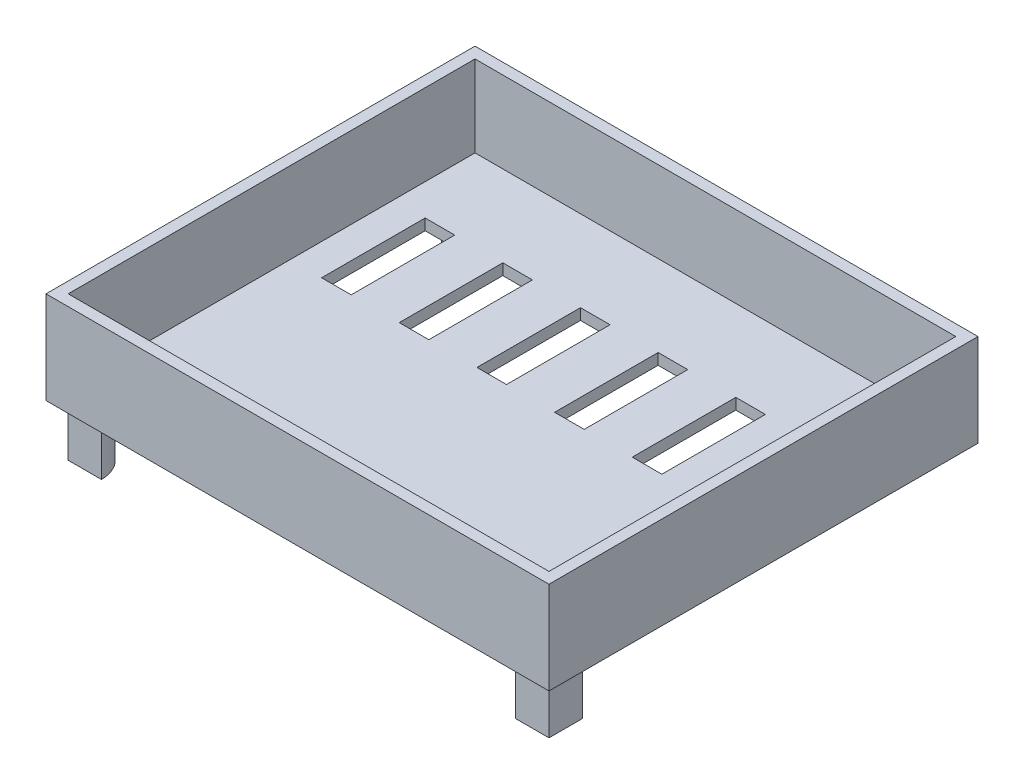
SolidWorks part; units mm, degrees
ref_plane "Front Plane" through (0, 0, 0) normal (0, 0, 1) x (1, 0, 0)
ref_plane "Top Plane" through (0, 0, 0) normal (0, 1, 0) x (1, 0, 0)
ref_plane "Right Plane" through (0, 0, 0) normal (1, 0, 0) x (0, 0, -1)
sketch "Sketch2" plane through (0, 0, 0) normal (0, 1, 0) x (1, 0, 0)
  line L1 (-58.7009, 58.1197) -> (77.2991, 58.1197)
  line L2 (-58.7009, 58.1197) -> (-58.7009, -77.8803)
  line L3 (-58.7009, -77.8803) -> (77.2991, -77.8803)
  line L4 (77.2991, 58.1197) -> (77.2991, -77.8803)
  dimension "D1" = 136
  dimension "D2" = 136
extrude "Boss-Extrude1" add sketch "Sketch2" along normal blind 25
sketch "Sketch3" plane through (0, 25, 0) normal (0, 1, 0) x (1, 0, 0)
  line L9 (-49.7009, -68.8803) -> (68.2991, -68.8803)
  line L10 (-49.7009, -68.8803) -> (-49.7009, 49.1197)
  line L11 (-49.7009, 49.1197) -> (68.2991, 49.1197)
  line L12 (68.2991, -68.8803) -> (68.2991, 49.1197)
extrude "Cut-Extrude1" cut sketch "Sketch3" against normal blind 22
sketch "Sketch4" plane through (0, 25, 0) normal (0, 1, 0) x (1, 0, 0)
  line L0 (77.2991, -77.8803) -> (47.2991, -77.8803)
  line L1 (-58.7009, -77.8803) -> (77.2991, -77.8803) construction
  line L2 (77.2991, -77.8803) -> (77.2991, -47.8803)
  line L3 (77.2991, -77.8803) -> (77.2991, 58.1197) construction
  line L4 (56.2991, -68.8803) -> (68.2991, -56.8803)
  line L5 (47.2991, -77.8803) -> (47.2991, -68.8803)
  line L6 (-49.7009, -68.8803) -> (68.2991, -68.8803) construction
  line L7 (47.2991, -68.8803) -> (56.2991, -68.8803)
  line L8 (77.2991, -47.8803) -> (68.2991, -47.8803)
  line L9 (68.2991, -68.8803) -> (68.2991, 49.1197) construction
  line L10 (68.2991, -47.8803) -> (68.2991, -56.8803)
extrude "Cut-Extrude3" cut sketch "Sketch4" against normal blind 22
sketch "Sketch5" plane through (0, 3, 0) normal (0, 1, 0) x (1, 0, 0)
  line L0 (68.2991, -47.8803) -> (47.2991, -68.8803)
  line L1 (47.2991, -68.8803) -> (47.2991, -77.8803)
  line L2 (47.2991, -77.8803) -> (77.2991, -77.8803)
  line L3 (77.2991, -77.8803) -> (77.2991, -47.8803)
  line L4 (77.2991, -47.8803) -> (68.2991, -47.8803)
extrude "Cut-Extrude4" cut sketch "Sketch5" against normal blind 22
sketch "Sketch7" plane through (58.0897, 0, 58.0897) normal (0.7071, 0, 0.7071) x (0.7071, 0, -0.7071)
  line L0 (-15.2602, 3) -> (14.4383, 3)
  line L1 (-15.2602, 3) -> (-15.2602, -27.0039)
  line L2 (14.4383, 3) -> (14.4383, -27.0039)
  line L3 (-15.2602, -27.0039) -> (14.4383, -27.0039)
extrude "Boss-Extrude2" add sketch "Sketch7" along normal blind 25
sketch "Sketch8" plane through (0, 3, 0) normal (0, 1, 0) x (1, 0, 0)
  line L0 (47.2991, -77.8803) -> (77.2991, -47.8803)
  line L1 (77.2991, -47.8803) -> (68.2991, -47.8803)
  line L2 (68.2991, -47.8803) -> (47.2991, -68.8803)
  line L3 (47.2991, -68.8803) -> (47.2991, -77.8803)
extrude "Boss-Extrude3" add sketch "Sketch8" against normal blind 3
sketch "Sketch9" plane through (0, 3, 0) normal (0, 1, 0) x (1, 0, 0)
  line L0 (47.2991, -77.8803) -> (38.2991, -68.8803)
  line L1 (-49.7009, -68.8803) -> (47.2991, -68.8803) construction
  line L2 (38.2991, -68.8803) -> (47.2991, -68.8803)
  line L3 (47.2991, -68.8803) -> (47.2991, -77.8803)
extrude "Cut-Extrude5" cut sketch "Sketch9" along normal blind 23
sketch "Sketch10" plane through (0, 25, 0) normal (0, 1, 0) x (1, 0, 0)
  line L0 (77.2991, -47.8803) -> (68.2991, -38.8803)
  line L1 (68.2991, -47.8803) -> (68.2991, 49.1197) construction
  line L2 (68.2991, -38.8803) -> (68.2991, -47.8803)
  line L3 (68.2991, -47.8803) -> (77.2991, -47.8803)
extrude "Cut-Extrude6" cut sketch "Sketch10" against normal blind 22
sketch "Sketch11" plane through (-10.7906, 0, 10.7906) normal (-0.7071, 0, 0.7071) x (0.7071, 0, 0.7071)
  line L0 (88.5153, 0) -> (107.1513, -18.636)
  line L1 (107.1513, 3) -> (107.1513, -27.0039) construction
  line L2 (107.1513, -18.636) -> (107.1513, -27.0039)
  line L3 (107.1513, -27.0039) -> (82.1513, -27.0039)
  line L4 (82.1513, -27.0039) -> (82.1513, 0)
  line L5 (82.1513, 0) -> (88.5153, 0)
  line L6 (88.5153, 3) -> (107.1513, -15.636)
  line L7 (107.1513, -15.636) -> (107.1513, 3)
  line L8 (107.1513, 3) -> (88.5153, 3)
extrude "Cut-Extrude7" cut sketch "Sketch11" against normal blind 32
sketch "Sketch16" plane through (-10.7906, 0, 10.7906) normal (-0.7071, 0, 0.7071) x (0.7071, 0, 0.7071)
  line L0 (88.5153, 0) -> (88.5153, 3)
  line L1 (88.5153, 3) -> (107.1513, -15.636)
  line L2 (107.1513, -15.636) -> (107.1513, -18.636)
  line L3 (107.1513, -18.636) -> (88.5153, 0)
extrude "Boss-Extrude6" add sketch "Sketch16" along normal blind 6.36
sketch "Sketch17" plane through (10.2094, 0, -10.2094) normal (0.7071, 0, -0.7071) x (-0.7071, 0, -0.7071)
  line L4 (-88.5153, 0) -> (-88.5153, 3)
  line L5 (-88.5153, 3) -> (-107.1513, -15.636)
  line L6 (-107.1513, -15.636) -> (-107.1513, -18.636)
  line L7 (-107.1513, -18.636) -> (-88.5153, 0)
  line L8 (-88.5153, 0) -> (-88.5153, 3)
  line L9 (-88.5153, 3) -> (-107.1513, -15.636)
  line L10 (-107.1513, -15.636) -> (-107.1513, -18.636)
  line L11 (-107.1513, -18.636) -> (-88.5153, 0)
  dimension "D1" = 0
extrude "Boss-Extrude7" add sketch "Sketch17" along normal blind 6.36
sketch "Sketch18" plane through (32.3555, 45.7576, 32.3555) normal (0.5, 0.7071, 0.5) x (0.866, -0.4082, -0.2887)
  line L0 (51.8932, -37.3644) -> (67.1094, -58.8834)
  line L1 (61.9165, -62.5554) -> (51.8932, -37.3644)
  line L3 (67.1094, -58.8834) -> (61.9165, -62.5554)
  line L4 (67.1094, -58.8834) -> (32.4749, -83.3737) construction
  line L5 (32.4749, -83.3737) -> (37.6678, -79.7018)
  line L6 (32.4749, -83.3737) -> (17.2586, -61.8547)
  line L7 (17.2586, -61.8547) -> (37.6678, -79.7018)
extrude "Cut-Extrude9" cut sketch "Sketch18" against normal blind 6.36
sketch "Sketch19" plane through (-15.2878, 0, 15.2878) normal (-0.7071, 0, 0.7071) x (0.7071, 0, 0.7071)
  line L3 (107.1513, -18.636) -> (107.1513, -15.636)
  line L4 (107.1513, -15.636) -> (105.6513, -17.136)
  line L5 (105.6513, -17.136) -> (107.1513, -18.636)
  line L6 (107.1513, -18.636) -> (107.1513, -15.636)
  line L7 (107.1513, -15.636) -> (105.6513, -17.136)
  line L8 (105.6513, -17.136) -> (107.1513, -18.636)
  dimension "D1" = 0
extrude "Cut-Extrude10" cut sketch "Sketch19" against normal blind 56.36
sketch "Sketch20" plane through (0, 0, 0) normal (0, -1, 0) x (1, 0, 0)
  line L0 (-58.7009, 77.8803) -> (47.2991, 77.8803)
  line L1 (47.2991, 77.8803) -> (77.2991, 47.8803)
  line L2 (77.2991, 47.8803) -> (77.2991, -58.1197)
  line L3 (77.2991, -58.1197) -> (-58.7009, -58.1197)
  line L4 (-58.7009, -58.1197) -> (-58.7009, 77.8803)
extrude "Boss-Extrude8" add sketch "Sketch20" against normal blind 3
sketch "Sketch22" plane through (0, 3, 0) normal (0, 1, 0) x (1, 0, 0)
  line L0 (64.9768, -86.558) -> (70.9062, -91.9285)
  line L1 (85.9768, -65.558) -> (91.9062, -70.9285)
  line L2 (70.9062, -91.9285) -> (91.9062, -70.9285)
  line L3 (64.9768, -86.558) -> (85.9768, -65.558)
extrude "Boss-Extrude9" add sketch "Sketch22" along normal blind 2 from offset 20 separate body offset against normal yes
sketch "Sketch23" plane through (75.7674, 0, 75.7674) normal (-0.7071, 0, -0.7071) x (-0.7071, 0, 0.7071)
  line L4 (-14.4383, -17) -> (15.2602, -17)
  line L5 (15.2602, -17) -> (15.2602, -15)
  line L6 (15.2602, -15) -> (-14.4383, -15)
  line L7 (-14.4383, -15) -> (-14.4383, -17)
  line L8 (-14.4383, -17) -> (15.2602, -17)
  line L9 (15.2602, -17) -> (15.2602, -15)
  line L10 (15.2602, -15) -> (-14.4383, -15)
  line L11 (-14.4383, -15) -> (-14.4383, -17)
  dimension "D1" = 0
extrude "Boss-Extrude10" add sketch "Sketch23" along normal blind 1.5
sketch "Sketch24" plane through (-13.7855, 0, 15.2203) normal (-0.6713, 0, 0.7412) x (0.7412, 0, 0.6713)
  line L0 (114.2665, -17) -> (103.9051, -17)
  line L1 (103.9051, -17) -> (103.9051, -17.7341)
  line L2 (103.9051, -17.7341) -> (114.2665, -17.7341)
  line L3 (114.2665, -17.7341) -> (114.2665, -17)
extrude "Cut-Extrude11" cut sketch "Sketch24" against normal blind 31.5
sketch "Sketch28" plane through (32.3555, 45.7576, 32.3555) normal (0.5, 0.7071, 0.5) x (0.866, -0.4082, -0.2887)
  line L2 (17.2554, -61.857) -> (8.1481, -53.8957)
  line L6 (51.8932, -37.3644) -> (47.3399, -25.921)
  line L7 (47.3399, -25.921) -> (8.1481, -53.8957)
  line L8 (17.2554, -61.857) -> (51.8932, -37.3644)
extrude "Boss-Extrude11" add sketch "Sketch28" against normal blind 4
sketch "Sketch29" plane through (14.7094, 0, -14.7094) normal (-0.7071, 0, 0.7071) x (0.7071, 0, 0.7071)
  line L0 (80.0587, 11.4566) -> (75.7873, 11.4566)
  line L1 (75.7873, 3) -> (75.7873, 25) construction
  line L2 (75.7873, 11.4566) -> (75.7873, 3)
  line L3 (75.7873, 3) -> (82.8584, 3)
  line L4 (82.8584, 3) -> (80.0587, 11.4566)
extrude "Boss-Extrude12" add sketch "Sketch29" along normal blind 44
sketch "Sketch30" plane through (0, 25, 0) normal (0, 1, 0) x (1, 0, 0)
  line L0 (38.2991, -68.8803) -> (68.2991, -38.8803)
  line L1 (68.2991, -38.8803) -> (77.2991, -47.8803)
  line L2 (77.2991, -47.8803) -> (91.9062, -70.9285)
  line L3 (91.9062, -70.9285) -> (70.9062, -91.9285)
  line L4 (70.9062, -91.9285) -> (47.2991, -77.8803)
  line L5 (47.2991, -77.8803) -> (38.2991, -68.8803)
extrude "Cut-Extrude12" cut sketch "Sketch30" against normal blind 50
sketch "Sketch31" plane through (0, 3, 0) normal (0, 1, 0) x (1, 0, 0)
  line L0 (68.2991, -38.8803) -> (77.2991, -47.8803)
  line L1 (47.2991, -77.8803) -> (77.2991, -77.8803)
  line L2 (77.2991, -77.8803) -> (77.2991, -47.8803)
  line L3 (47.2991, -77.8803) -> (38.2991, -68.8803)
  line L4 (38.2991, -68.8803) -> (68.2991, -38.8803)
extrude "Boss-Extrude13" add sketch "Sketch31" against normal blind 3
sketch "Sketch32" plane through (0, 3, 0) normal (0, 1, 0) x (1, 0, 0)
  line L0 (77.2991, -77.8803) -> (77.2991, -47.8803)
  line L1 (77.2991, -47.8803) -> (68.2991, -38.8803)
  line L2 (77.2991, -77.8803) -> (47.2991, -77.8803)
  line L3 (47.2991, -77.8803) -> (38.2991, -68.8803)
  line L4 (38.2991, -68.8803) -> (68.2991, -68.8803)
  line L5 (68.2991, -68.8803) -> (68.2991, -38.8803)
extrude "Boss-Extrude14" add sketch "Sketch32" along normal blind 22
sketch "Sketch33" plane through (0, 25, 0) normal (0, 1, 0) x (1, 0, 0)
  line L9 (-55.7009, -74.8803) -> (74.2991, -74.8803)
  line L10 (-55.7009, -74.8803) -> (-55.7009, 55.1197)
  line L11 (-55.7009, 55.1197) -> (74.2991, 55.1197)
  line L12 (74.2991, -74.8803) -> (74.2991, 55.1197)
extrude "Cut-Extrude13" cut sketch "Sketch33" against normal blind 22
sketch "Sketch34" plane through (0, 3, 0) normal (0, 1, 0) x (1, 0, 0)
  line L43 (-43.2009, -14.8662) -> (-39.2009, -14.8662)
  line L44 (-43.2009, -14.8662) -> (-47.2009, -14.8662)
  line L45 (-22.2009, -14.8659) -> (-18.2009, -14.8659)
  line L47 (-1.2009, -14.8655) -> (2.7991, -14.8655)
  line L48 (19.7991, -14.8652) -> (23.7991, -14.8652)
  line L49 (40.7991, -14.8648) -> (44.7991, -14.8648)
  line L50 (61.7991, -14.8645) -> (65.7991, -14.8645)
  line L51 (-22.2009, -14.8659) -> (-26.2009, -14.8659)
  line L52 (-1.2009, -14.8655) -> (-5.2009, -14.8655)
  line L53 (19.7991, -14.8652) -> (15.7991, -14.8652)
  line L54 (40.7991, -14.8648) -> (36.7991, -14.8648)
  line L55 (61.7991, -14.8645) -> (57.7991, -14.8645)
  line L59 (-47.2009, -14.8662) -> (-47.2009, 13.1338)
  line L60 (-47.2009, 13.1338) -> (-39.2009, 13.1338)
  line L61 (-39.2009, 13.1338) -> (-39.2009, -14.8662)
  line L62 (-26.2009, -14.8659) -> (-26.2009, 13.1338)
  line L63 (-26.2009, 13.1338) -> (-18.2009, 13.1338)
  line L64 (-18.2009, 13.1338) -> (-18.2009, -14.8659)
  line L65 (-5.2009, -14.8655) -> (-5.2009, 13.1338)
  line L66 (-5.2009, 13.1338) -> (2.7991, 13.1338)
  line L67 (2.7991, 13.1338) -> (2.7991, -14.8655)
  line L68 (15.7991, -14.8652) -> (15.7991, 13.1338)
  line L69 (15.7991, 13.1338) -> (23.7991, 13.1338)
  line L70 (23.7991, 13.1338) -> (23.7991, -14.8652)
  line L71 (36.7991, -14.8648) -> (36.7991, 13.1338)
  line L72 (36.7991, 13.1338) -> (44.7991, 13.1338)
  line L73 (44.7991, 13.1338) -> (44.7991, -14.8648)
  line L74 (57.7991, -14.8645) -> (57.7991, 13.1338)
  line L75 (57.7991, 13.1338) -> (65.7991, 13.1338)
  line L76 (65.7991, 13.1338) -> (65.7991, -14.8645)
extrude "Cut-Extrude15" cut sketch "Sketch34" against normal blind 12
sketch "Sketch35" plane through (0, 25, 0) normal (0, 1, 0) x (1, 0, 0)
  line L1 (-55.7009, 55.1197) -> (-55.7009, -74.8803) construction
  line L2 (-55.7009, 35.1197) -> (77.2991, 35.1197)
  line L3 (77.2991, -77.8803) -> (77.2991, 58.1197) construction
  line L4 (77.2991, 35.1197) -> (77.2991, 58.1197)
  line L5 (77.2991, 58.1197) -> (-58.7009, 58.1197)
  line L6 (-58.7009, 58.1197) -> (-58.7009, 35.1197)
  line L7 (-58.7009, 58.1197) -> (-58.7009, -77.8803) construction
  line L8 (-58.7009, 35.1197) -> (-55.7009, 35.1197)
extrude "Cut-Extrude16" cut sketch "Sketch35" against normal blind 32
sketch "Sketch36" plane through (0, 3, 0) normal (0, 1, 0) x (1, 0, 0)
  line L0 (-58.7009, 35.1197) -> (-55.7009, 35.1197)
  line L1 (-58.7009, 35.1197) -> (-58.7009, 38.1197)
  line L2 (-58.7009, 38.1197) -> (77.2991, 38.1197)
  line L3 (77.2991, 35.1197) -> (77.2991, 38.1197)
  line L4 (77.2991, 35.1197) -> (-55.7009, 35.1197)
extrude "Boss-Extrude15" add sketch "Sketch36" along normal blind 22 and the other way blind 3
sketch "Sketch37" plane through (0, 0, 0) normal (0, -1, 0) x (1, 0, 0)
  line L0 (-55.7009, -35.1197) -> (-55.7009, -26.1197) construction
  line L1 (-55.7009, 74.8803) -> (-46.7009, 74.8803) construction
  line L2 (-49.7043, 74.8803) -> (-55.7009, 74.8803)
  line L3 (-55.7009, 74.8803) -> (-55.7009, 68.8838)
  line L4 (-55.7009, -35.1197) -> (-55.7009, 74.8803) construction
  line L5 (74.2991, -35.1197) -> (-55.7009, -35.1197) construction
  line L6 (-55.7009, -29.1197) -> (-55.7009, -35.1197)
  line L7 (-55.7009, -35.1197) -> (-49.7009, -35.1197)
  arc A0 (-55.7009, 68.8838) -> (-49.7043, 74.8803) centre (-55.7009, 74.8803) ccw
  arc A1 (-55.7009, -29.1197) -> (-49.7009, -35.1197) centre (-55.7009, -35.1197) cw
extrude "Boss-Extrude16" add sketch "Sketch37" along normal up to vertex (16.9804 mm away)
sketch "Sketch38" plane through (0, -16.9804, 0) normal (0, -1, 0) x (1, 0, 0)
  line L0 (-55.7009, 74.8803) -> (-55.7009, 68.8838) construction
  line L1 (-49.7043, 74.8803) -> (-55.7009, 74.8803) construction
  line L2 (-55.7009, -35.1197) -> (-49.7009, -35.1197) construction
  line L3 (-55.7009, -29.1197) -> (-55.7009, -35.1197) construction
  line L4 (-55.7009, 74.8803) -> (-55.7009, 68.8838)
  line L5 (-49.7043, 74.8803) -> (-55.7009, 74.8803)
  line L6 (-55.7009, -35.1197) -> (-49.7009, -35.1197)
  line L7 (-55.7009, -29.1197) -> (-55.7009, -35.1197)
  arc A0 (-55.7009, 68.8838) -> (-49.7043, 74.8803) centre (-55.7009, 74.8803) ccw construction
  arc A1 (-49.7009, -35.1197) -> (-55.7009, -29.1197) centre (-55.7009, -35.1197) ccw construction
  arc A2 (-55.7009, 68.8838) -> (-49.7043, 74.8803) centre (-55.7009, 74.8803) ccw
  arc A3 (-49.7009, -35.1197) -> (-55.7009, -29.1197) centre (-55.7009, -35.1197) ccw
extrude "Cut-Extrude17" cut sketch "Sketch38" against normal blind 2
sketch "Sketch39" plane through (0, 0, 0) normal (0, -1, 0) x (1, 0, 0)
  line L0 (-55.7009, 74.8803) -> (-46.7009, 74.8803) construction
  line L1 (74.2991, 74.8803) -> (74.2991, 65.8803) construction
  line L2 (68.2991, 74.8803) -> (74.2991, 74.8803)
  line L3 (74.2991, 74.8803) -> (74.2991, 68.8803)
  arc A0 (68.2991, 74.8803) -> (74.2991, 68.8803) centre (74.2991, 74.8803) ccw
extrude "Boss-Extrude17" add sketch "Sketch39" along normal up to vertex (14.9804 mm away)
sketch "Sketch40" plane through (0, -14.9804, 0) normal (0, -1, 0) x (1, 0, 0)
  line L0 (74.2991, 68.8803) -> (74.2991, 74.8803) construction
  line L1 (74.2991, 74.8803) -> (68.2991, 74.8803) construction
  line L2 (-49.7043, 74.8803) -> (-55.7009, 74.8803) construction
  line L3 (-55.7009, 74.8803) -> (-55.7009, 68.8838) construction
  line L4 (-55.7009, -29.1197) -> (-55.7009, -35.1197) construction
  line L5 (-55.7009, -35.1197) -> (-49.7009, -35.1197) construction
  line L6 (74.2991, 68.8803) -> (74.2991, 74.8803)
  line L7 (74.2991, 74.8803) -> (68.2991, 74.8803)
  line L8 (-49.7043, 74.8803) -> (-55.7009, 74.8803)
  line L9 (-55.7009, 74.8803) -> (-55.7009, 68.8838)
  line L10 (-55.7009, -29.1197) -> (-55.7009, -35.1197)
  line L11 (-55.7009, -35.1197) -> (-49.7009, -35.1197)
  arc A0 (68.2991, 74.8803) -> (74.2991, 68.8803) centre (74.2991, 74.8803) ccw construction
  arc A1 (-55.7009, 68.8838) -> (-49.7043, 74.8803) centre (-55.7009, 74.8803) ccw construction
  arc A2 (-49.7009, -35.1197) -> (-55.7009, -29.1197) centre (-55.7009, -35.1197) ccw construction
  arc A3 (68.2991, 74.8803) -> (74.2991, 68.8803) centre (74.2991, 74.8803) ccw
  arc A4 (-55.7009, 68.8838) -> (-49.7043, 74.8803) centre (-55.7009, 74.8803) ccw
  arc A5 (-49.7009, -35.1197) -> (-55.7009, -29.1197) centre (-55.7009, -35.1197) ccw
extrude "Cut-Extrude18" cut sketch "Sketch40" against normal blind 1
sketch "Sketch42" plane through (0, -13.9804, 0) normal (0, -1, 0) x (-1, 0, 0)
  line L0 (55.7009, 35.1197) -> (55.7009, 26.1197) construction
  line L1 (55.7009, -74.8803) -> (46.7009, -74.8803) construction
  line L2 (55.7009, -65.8803) -> (55.7009, -74.8803)
  line L3 (55.7009, -74.8803) -> (46.7009, -74.8803)
  line L4 (46.7009, 35.1197) -> (55.7009, 35.1197) construction
  line L5 (55.7009, 26.1197) -> (55.7009, 35.1197)
  line L6 (55.7009, 35.1197) -> (46.7009, 35.1197)
  line L7 (-74.2991, -74.8803) -> (-74.2991, -65.8803) construction
  line L8 (-65.2991, -74.8803) -> (-74.2991, -74.8803)
  line L9 (-74.2991, -74.8803) -> (-74.2991, -65.8803)
  arc A0 (55.7009, -65.8803) -> (46.7009, -74.8803) centre (55.7009, -74.8803) ccw
  arc A1 (46.7009, 35.1197) -> (55.7009, 26.1197) centre (55.7009, 35.1197) ccw
  arc A2 (-74.2991, -65.8803) -> (-65.2991, -74.8803) centre (-74.2991, -74.8803) cw
extrude "Boss-Extrude20" add sketch "Sketch42" against normal up to surface (13.9804 mm away) up to face at (71.8849, 0, 72.4661)
sketch "Sketch43" plane through (0, 25, 0) normal (0, 1, 0) x (1, 0, 0)
  line L0 (-55.7009, -74.8803) -> (74.2991, -74.8803) construction
  line L1 (74.2991, -74.8803) -> (74.2991, 35.1197) construction
  line L2 (-55.7009, 35.1197) -> (74.2991, 35.1197) construction
  line L3 (-55.7009, 35.1197) -> (-55.7009, -74.8803) construction
  line L4 (77.2991, 38.1197) -> (-58.7009, 38.1197)
  line L5 (-58.7009, 38.1197) -> (-58.7009, -77.8803)
  line L6 (-58.7009, -77.8803) -> (77.2991, -77.8803)
  line L7 (77.2991, -77.8803) -> (77.2991, 38.1197)
  line L8 (77.2991, 38.1197) -> (-58.7009, 38.1197)
  line L9 (-58.7009, 38.1197) -> (-58.7009, -77.8803)
  line L10 (-58.7009, -77.8803) -> (77.2991, -77.8803)
  line L11 (77.2991, -77.8803) -> (77.2991, 38.1197)
  line L12 (-55.7009, -74.8803) -> (74.2991, -74.8803)
  line L13 (74.2991, -74.8803) -> (74.2991, 35.1197)
  line L14 (-55.7009, 35.1197) -> (74.2991, 35.1197)
  line L15 (-55.7009, 35.1197) -> (-55.7009, -74.8803)
  dimension "D1" = 0
